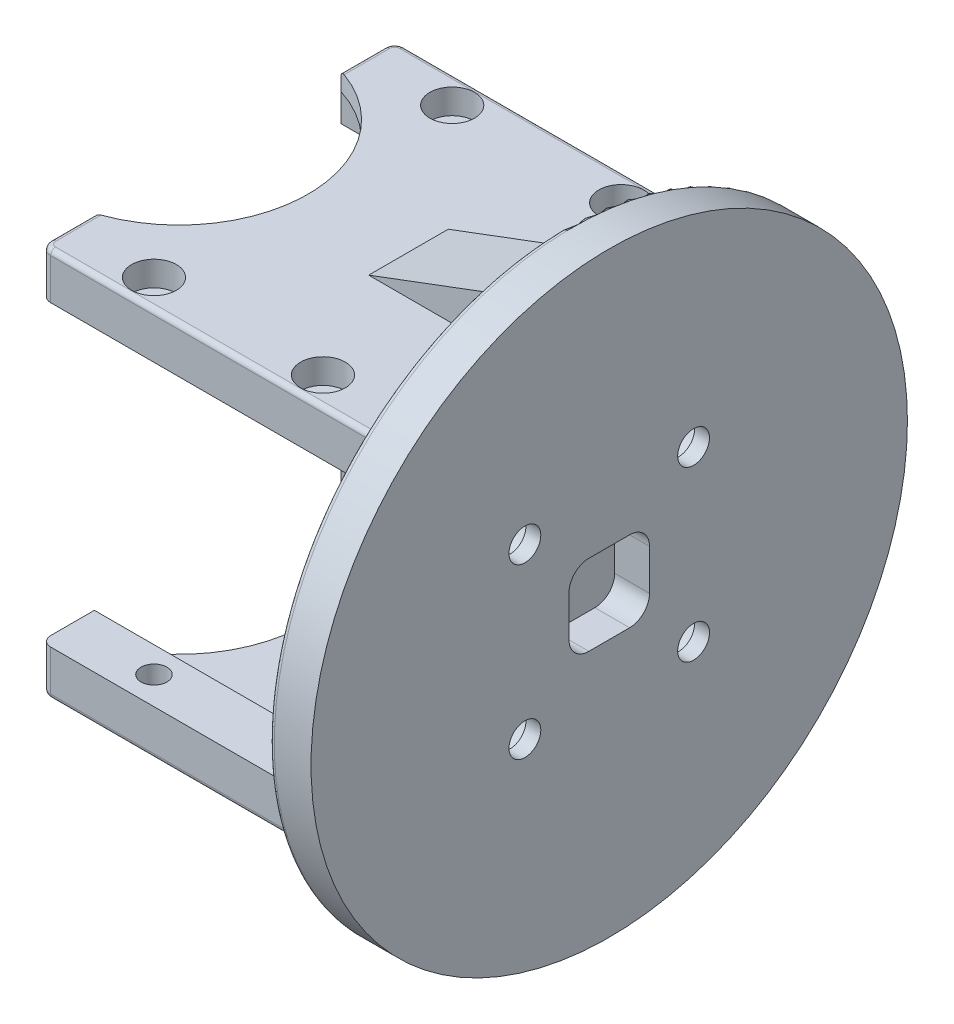
SolidWorks part; units mm, degrees
ref_plane "Front Plane" through (0, 0, 0) normal (0, 0, 1) x (1, 0, 0)
ref_plane "Top Plane" through (0, 0, 0) normal (0, 1, 0) x (1, 0, 0)
ref_plane "Right Plane" through (0, 0, 0) normal (1, 0, 0) x (0, 0, -1)
sketch "Sketch1" plane through (0, 0, 0) normal (0, 1, 0) x (1, 0, 0)
  line L0 (0, 0) -> (0, 15) construction
  line L1 (0, 15) -> (-4.5, 15) construction
  line L2 (0, 0) -> (12.5, 0) construction
  line L3 (-4.5, 12.4) -> (33.2, 12.4) construction
  line L4 (33.2, 12.4) -> (33.2, -12.4)
  line L5 (-4.5, 17.8) -> (38.3, 17.8) construction
  line L6 (38.3, 17.8) -> (38.3, -17.8)
  line L7 (33.2, 0) -> (38.3, 0) construction
  line L8 (-4.5, -12.4) -> (33.2, -12.4) construction
  line L9 (-4.5, -17.8) -> (38.3, -17.8) construction
  line L10 (-4.5, 17.8) -> (-12.2, 17.8) construction
  line L12 (-12.2, 12.4) -> (-4.5, 12.4) construction
  line L13 (-12.2, -12.4) -> (-4.5, -12.4) construction
  line L16 (-12.2, 12.4) -> (-12.2, -12.4) construction
  line L26 (3.9038, 12.4) -> (3.9038, 17.8)
  line L27 (3.9038, 17.8) -> (38.3, 17.8)
  line L28 (3.9038, -12.4) -> (3.9038, -17.8)
  line L29 (3.9038, -17.8) -> (38.3, -17.8)
  line L30 (3.9038, 12.4) -> (33.2, 12.4)
  line L31 (3.9038, -12.4) -> (33.2, -12.4)
  circle A0 centre (-4.5, 15) radius 1.3 construction
  circle A1 centre (12.5, 15) radius 1.3
  circle A2 centre (29.5, 15) radius 1.3
  circle A4 centre (29.5, -15) radius 1.3
  circle A5 centre (12.5, -15) radius 1.3
  circle A6 centre (-4.5, -15) radius 1.3 construction
  circle A8 centre (0, 0) radius 11 construction
  circle A9 centre (-4.5, 15) radius 2.25 construction
  arc A14 (3.9038, 12.4) -> (3.9038, -12.4) centre (0, 0) cw construction
  circle A15 centre (35.8, -8.5) radius 1.3
  circle A16 centre (35.8, 8.5) radius 1.3
  dimension "D4" = 2.6
  dimension "D12" = 22
  dimension "D13" = 4.5
  dimension "D16" = 6.5
  dimension "D15" = 6.3
  dimension "D14" = 13
  dimension "D1" = 15
  dimension "D2" = 4.5
  dimension "D3" = 17
  dimension "D6" = 2.6
  dimension "D7" = 34
  dimension "D8" = 3.7
  dimension "D9" = 2.8
  dimension "D10" = 5.1
  dimension "D11" = 7.7
  dimension "D5" = 3
extrude "Boss-Extrude1" add sketch "Sketch1" along normal blind 2.8
sketch "Sketch2" plane through (0, 2.8, 0) normal (0, 1, 0) x (1, 0, 0)
  line L0 (3.9038, -12.4) -> (3.9038, -17.8) construction
  line L1 (3.9038, -17.8) -> (38.3, -17.8) construction
  line L2 (38.3, 17.8) -> (38.3, -17.8) construction
  line L3 (3.9038, 17.8) -> (38.3, 17.8) construction
  line L4 (3.9038, 12.4) -> (3.9038, 17.8) construction
  line L5 (3.9038, -12.4) -> (3.9038, -17.8)
  line L6 (3.9038, -17.8) -> (38.3, -17.8)
  line L7 (38.3, 17.8) -> (38.3, -17.8)
  line L8 (3.9038, 17.8) -> (38.3, 17.8)
  line L9 (3.9038, 12.4) -> (3.9038, 17.8)
  arc A0 (3.9038, -12.4) -> (3.9038, 12.4) centre (0, 0) ccw construction
  arc A1 (3.9038, -12.4) -> (3.9038, 12.4) centre (0, 0) ccw
  circle A2 centre (12.5, -15) radius 1.3 construction
  circle A3 centre (29.5, -15) radius 1.3 construction
  circle A4 centre (35.8, -8.5) radius 1.3 construction
  circle A5 centre (35.8, 8.5) radius 1.3 construction
  circle A6 centre (29.5, 15) radius 1.3 construction
  circle A7 centre (12.5, 15) radius 1.3 construction
  circle A8 centre (12.5, -15) radius 1.3
  circle A9 centre (29.5, -15) radius 1.3
  circle A10 centre (35.8, -8.5) radius 1.3
  circle A11 centre (35.8, 8.5) radius 1.3
  circle A12 centre (29.5, 15) radius 1.3
  circle A13 centre (12.5, 15) radius 1.3
extrude "Boss-Extrude2" add sketch "Sketch2" along normal blind 1.8
sketch "Sketch3" plane through (0, 4.6, 0) normal (0, 1, 0) x (1, 0, 0)
  line L0 (0, 0) -> (38.3, 0) construction
  line L1 (38.3, -17.8) -> (38.3, 17.8) construction
  circle A0 centre (35.8, 8.5) radius 1.3 construction
  circle A1 centre (29.5, 15) radius 1.3 construction
  circle A2 centre (12.5, 15) radius 1.3 construction
  circle A3 centre (35.8, 8.5) radius 1.3 construction
  circle A4 centre (29.5, 15) radius 1.3 construction
  circle A5 centre (12.5, 15) radius 1.3 construction
  circle A6 centre (12.5, 15) radius 2.25
  circle A7 centre (29.5, 15) radius 2.25
  circle A8 centre (35.8, 8.5) radius 2.25
  circle A9 centre (35.8, -8.5) radius 2.25
  circle A10 centre (29.5, -15) radius 2.25
  circle A11 centre (12.5, -15) radius 2.25
  dimension "D1" = 4.5
extrude "Cut-Extrude1" cut sketch "Sketch3" against normal blind 2.5
sketch "Sketch4" plane through (38.3, 0, 0) normal (1, 0, 0) x (0, 0, -1)
  line L4 (-17.8, 0) -> (17.8, 0)
  line L5 (17.8, 0) -> (17.8, 4.6)
  line L6 (17.8, 4.6) -> (-17.8, 4.6)
  line L7 (-17.8, 4.6) -> (-17.8, 0)
  line L8 (-17.8, 0) -> (17.8, 0)
  line L9 (17.8, 0) -> (17.8, 4.6)
  line L10 (17.8, 4.6) -> (-17.8, 4.6)
  line L11 (-17.8, 4.6) -> (-17.8, 0)
  dimension "D1" = 0
extrude "Boss-Extrude3" add sketch "Sketch4" along normal blind 5
sketch "Sketch5" plane through (0, 0, 0) normal (0, -1, 0) x (1, 0, 0)
  line L0 (43.3, -17.8) -> (3.9038, -17.8) construction
  line L1 (43.3, 17.8) -> (39.1, 17.8)
  line L2 (43.3, 17.8) -> (43.3, -17.8)
  line L3 (43.3, -17.8) -> (39.1, -17.8)
  line L4 (39.1, 17.8) -> (39.1, -17.8)
  dimension "D1" = 4.2
extrude "Boss-Extrude4" add sketch "Sketch5" along normal blind 15
mirror "Mirror1" about plane through (0, -15, 0) normal (0, 1, 0) of bodies 117
fillet "Fillet1" radius 1 4 edges at (3.9038, 2.3, -17.8) (3.9038, 2.3, 17.8) (3.9038, -32.3, 17.8) (3.9038, -32.3, -17.8)
sketch "Sketch6" plane through (43.3, 0, 0) normal (1, 0, 0) x (0, 0, -1)
  line L0 (17.8, -15) -> (0, -15) construction
  line L1 (17.8, -34.6) -> (17.8, 4.6) construction
  line L2 (0, -15) -> (0, -34.6) construction
  line L3 (17.8, -34.6) -> (-17.8, -34.6) construction
  line L4 (0, -15) -> (8.4853, -23.4853) construction
  circle A0 centre (0, -15) radius 12 construction
  circle A1 centre (8.4853, -23.4853) radius 1.6
  circle A2 centre (-8.4853, -23.4853) radius 1.6
  circle A3 centre (-8.4853, -6.5147) radius 1.6
  circle A4 centre (8.4853, -6.5147) radius 1.6
  point P19 (0, -15)
  dimension "D1" = 24
  dimension "D3" = 3.2
  dimension "D2" = 45
  dimension "D4" = 4
extrude "Cut-Extrude2" cut sketch "Sketch6" against normal through all
sketch "Sketch7" plane through (39.1, 0, 0) normal (-1, 0, 0) x (0, 0, 1)
  circle A0 centre (-8.4853, -6.5147) radius 1.6 construction
  circle A1 centre (-8.4853, -6.5147) radius 1.6 construction
  circle A2 centre (8.4853, -23.4853) radius 1.6 construction
  circle A3 centre (8.4853, -23.4853) radius 1.6 construction
  circle A4 centre (-8.4853, -23.4853) radius 1.6 construction
  circle A5 centre (8.4853, -6.5147) radius 1.6 construction
  circle A6 centre (-8.4853, -23.4853) radius 1.6 construction
  circle A7 centre (8.4853, -6.5147) radius 1.6 construction
  circle A8 centre (-8.4853, -6.5147) radius 2.8
  circle A9 centre (8.4853, -6.5147) radius 2.8
  circle A10 centre (-8.4853, -23.4853) radius 2.8
  circle A11 centre (8.4853, -23.4853) radius 2.8
  dimension "D1" = 5.6
extrude "Cut-Extrude3" cut sketch "Sketch7" against normal blind 2.7
sketch "Sketch8" plane through (43.3, 0, 0) normal (1, 0, 0) x (0, 0, -1)
  line L0 (-17.8, -15) -> (0, -15) construction
  line L1 (-17.8, 4.6) -> (-17.8, -34.6) construction
  line L2 (0, -15) -> (0, 0) construction
  line L4 (-2.05, -19.05) -> (2.05, -19.05)
  line L5 (-4.05, -17.05) -> (-4.05, -12.95)
  line L6 (-2.05, -10.95) -> (2.05, -10.95)
  line L7 (4.05, -17.05) -> (4.05, -12.95)
  line L8 (-4.05, -19.05) -> (4.05, -10.95) construction
  line L9 (-4.05, -10.95) -> (4.05, -19.05) construction
  arc A0 (2.05, -19.05) -> (4.05, -17.05) centre (2.05, -17.05) ccw
  arc A1 (-2.05, -19.05) -> (-4.05, -17.05) centre (-2.05, -17.05) cw
  arc A2 (2.05, -10.95) -> (4.05, -12.95) centre (2.05, -12.95) cw
  arc A3 (-4.05, -12.95) -> (-2.05, -10.95) centre (-2.05, -12.95) cw
  dimension "D2" = 2
  dimension "D1" = 8.1
extrude "Cut-Extrude4" cut sketch "Sketch8" against normal blind 3.5
sketch "Sketch9" plane through (43.3, 0, 0) normal (1, 0, 0) x (0, 0, -1)
  line L0 (0, -15) -> (0, 0) construction
  line L1 (0, -15) -> (-17.8, -15) construction
  line L2 (-17.8, 4.6) -> (-17.8, -34.6) construction
  line L3 (17.8, -34.6) -> (17.8, 4.6) construction
  line L4 (17.8, -34.6) -> (-17.8, -34.6) construction
  line L5 (17.8, 4.6) -> (-17.8, 4.6) construction
  line L6 (17.8, -34.6) -> (17.8, 4.6)
  line L7 (17.8, -34.6) -> (-17.8, -34.6)
  line L8 (-17.8, 4.6) -> (-17.8, -34.6)
  line L9 (17.8, 4.6) -> (-17.8, 4.6)
  circle A0 centre (0, -15) radius 30
  dimension "D1" = 60
extrude "Boss-Extrude5" add sketch "Sketch9" against normal up to surface (4.2 mm away) up to face at (39.1, -6.5147, 11.2853)
sketch "Sketch10" plane through (0, 0, 0) normal (0, 0, 1) x (1, 0, 0)
  line L0 (39.1, 10.6) -> (39.1, 4.6)
  line L1 (39.1, 4.6) -> (23.1, 4.6)
  line L2 (4.9038, 4.6) -> (39.1, 4.6) construction
  line L3 (23.1, 4.6) -> (39.1, 10.6)
  dimension "D1" = 6
  dimension "D2" = 16
extrude "Boss-Extrude6" add sketch "Sketch10" along normal mid plane 8
ref_plane "Plane1" through (0, -15, 0) normal (0, -1, 0) x (-1, 0, 0)
mirror "Mirror2" about plane through (0, -15, 0) normal (0, -1, 0) of "Boss-Extrude6"
fillet "Fillet2" radius 0.5 1 edges at (39.1, -15, -30)
fillet "Fillet3" radius 0.5 26 edges at (3.9038, -34.6, 14.6) (4.1967, -34.6, 17.5071) (3.9038, -34.6, -14.6) (4.1967, -34.6, -17.5071) (3.9038, 4.6, 14.6) (4.1967, 4.6, 17.5071) (3.9038, 4.6, -14.6) (4.1967, 4.6, -17.5071) (22.0019, -34.6, 17.8) (22.0019, -34.6, -17.8) (39.1, -32.3, -17.8) (39.1, -37.6, 4) (39.1, -32.3, 17.8) (39.1, -34.6, 10.9) (39.1, -40.6, 0) (39.1, -34.6, -10.9) (39.1, -37.6, -4) (22.0019, 4.6, 17.8) (22.0019, 4.6, -17.8) (39.1, 2.3, 17.8) (39.1, 4.6, 10.9) (39.1, 7.6, 4) (39.1, 10.6, 0) (39.1, 2.3, -17.8) (39.1, 4.6, -10.9) (39.1, 7.6, -4)
